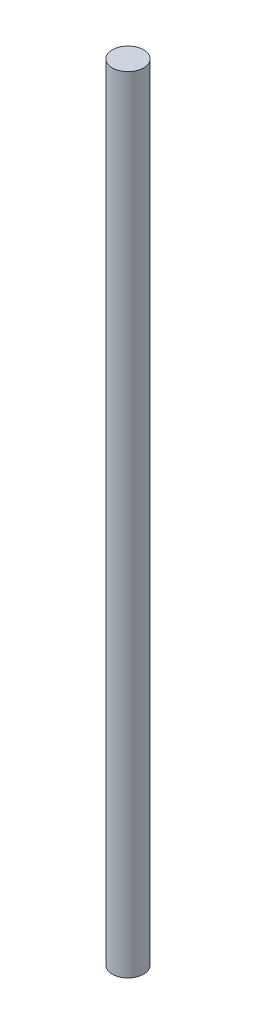
SolidWorks part; units mm, degrees
ref_plane "Front Plane" through (0, 0, 0) normal (0, 0, 1) x (1, 0, 0)
ref_plane "Top Plane" through (0, 0, 0) normal (0, 1, 0) x (1, 0, 0)
ref_plane "Right Plane" through (0, 0, 0) normal (1, 0, 0) x (0, 0, -1)
sketch "Sketch1" plane through (0, 0, 0) normal (0, 1, 0) x (1, 0, 0)
  circle A0 centre (0, 0) radius 2.54
  dimension "D1" = 5.08
extrude "Boss-Extrude1" add sketch "Sketch1" along normal blind 127
